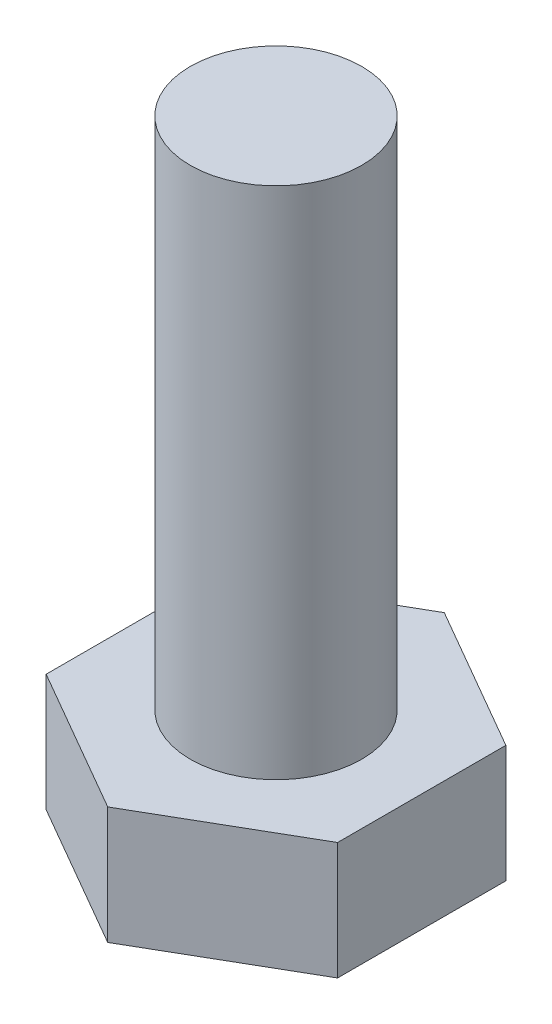
SolidWorks part; units mm, degrees
ref_plane "Спереди" through (0, 0, 0) normal (0, 0, 1) x (1, 0, 0)
ref_plane "Сверху" through (0, 0, 0) normal (0, 1, 0) x (1, 0, 0)
ref_plane "Справа" through (0, 0, 0) normal (1, 0, 0) x (0, 0, -1)
sketch "Эскиз1" plane through (0, 0, 0) normal (0, 1, 0) x (1, 0, 0)
  line L1 (8.5, -4.9075) -> (8.5, 4.9075)
  line L2 (8.5, 4.9075) -> (0, 9.815)
  line L3 (0, 9.815) -> (-8.5, 4.9075)
  line L4 (-8.5, 4.9075) -> (-8.5, -4.9075)
  line L5 (-8.5, -4.9075) -> (0, -9.815)
  line L6 (0, -9.815) -> (8.5, -4.9075)
  circle A0 centre (0, 0) radius 8.5 construction
extrude "Бобышка-Вытянуть1" add sketch "Эскиз1" along normal blind 8
sketch "Эскиз2" plane through (0, 8, 0) normal (0, 1, 0) x (1, 0, 0)
  circle A0 centre (0, 0) radius 5
extrude "Бобышка-Вытянуть2" add sketch "Эскиз2" along normal blind 30
chamfer "Фаска1" distance 2 angle 30 6 edges at (4.25, 0, -7.3612) (8.5, 0, 0) (4.25, 0, 7.3612) (-4.25, 0, 7.3612) (-8.5, 0, 0) (-4.25, 0, -7.3612)
